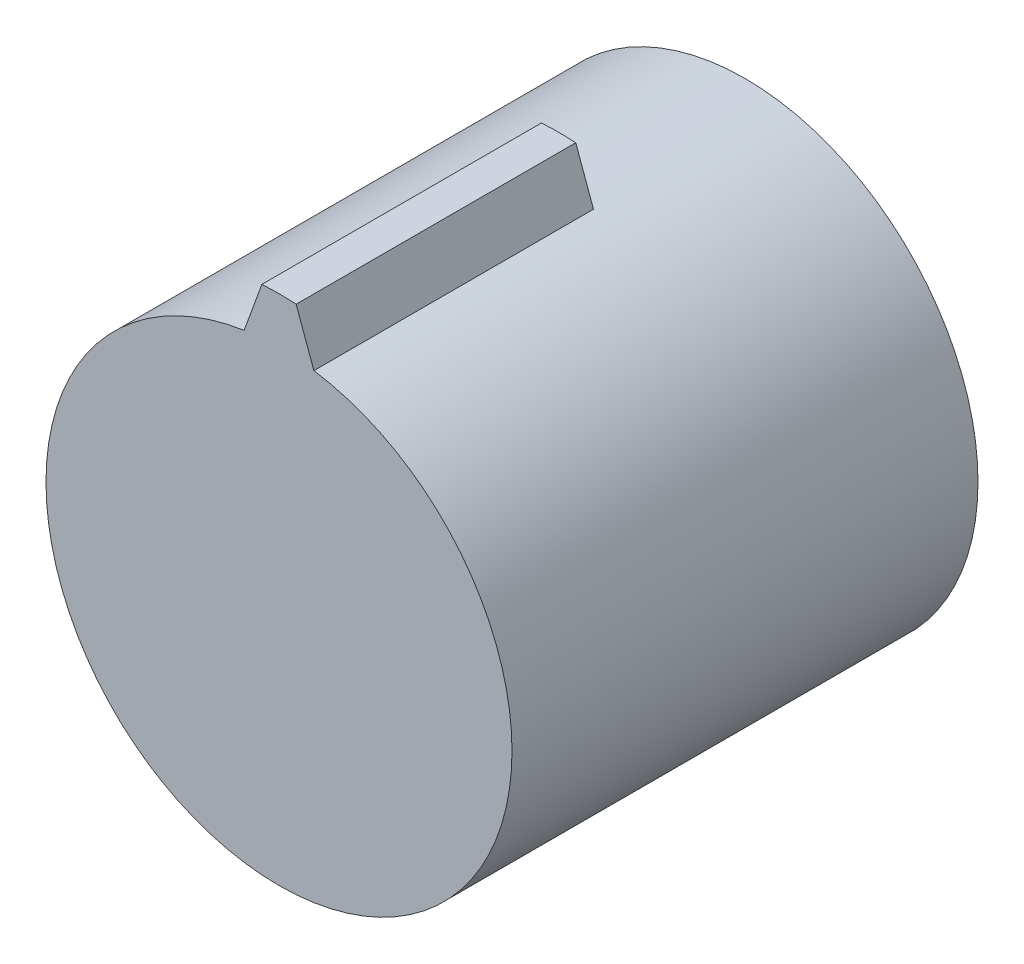
SolidWorks part; units mm, degrees
ref_plane "前视基准面" through (0, 0, 0) normal (0, 0, 1) x (1, 0, 0)
ref_plane "上视基准面" through (0, 0, 0) normal (0, 1, 0) x (1, 0, 0)
ref_plane "右视基准面" through (0, 0, 0) normal (1, 0, 0) x (0, 0, -1)
sketch "草图1" plane through (0, 0, 0) normal (0, 0, 1) x (1, 0, 0)
  circle A0 centre (0, 0) radius 2.5
  dimension "D1" = 5
extrude "凸台-拉伸1" add sketch "草图1" along normal blind 5
sketch "草图2" plane through (0, 0, 5) normal (0, 0, 1) x (1, 0, 0)
  line L0 (0, 0) -> (0, 3) construction
  line L1 (-0.184, 2.9943) -> (-0.3742, 2.4718)
  line L2 (0.184, 2.9943) -> (0.3742, 2.4718)
  arc A0 (0.184, 2.9943) -> (-0.184, 2.9943) centre (0, 0) ccw
  circle A1 centre (0, 0) radius 2.5
  arc A2 (0.3742, 2.4718) -> (-0.3742, 2.4718) centre (0, 0) ccw
  dimension "D2" = 6
  dimension "D4" = 40
  dimension "D1" = 0
extrude "凸台-拉伸2" add sketch "草图2" against normal blind 3
